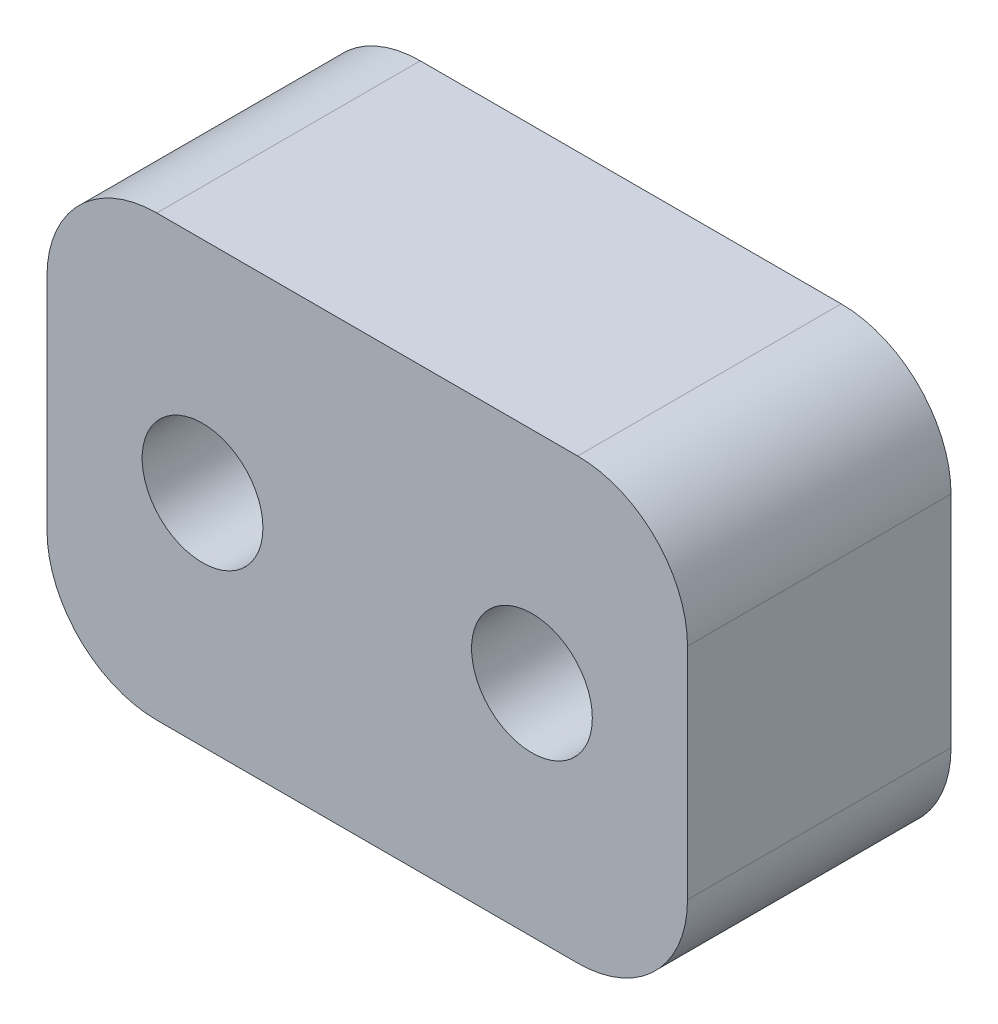
SolidWorks part; units mm, degrees
ref_plane "Front Plane" through (0, 0, 0) normal (0, 0, 1) x (1, 0, 0)
ref_plane "Top Plane" through (0, 0, 0) normal (0, 1, 0) x (1, 0, 0)
ref_plane "Right Plane" through (0, 0, 0) normal (1, 0, 0) x (0, 0, -1)
sketch "Sketch1" plane through (0, 0, 0) normal (0, 0, 1) x (1, 0, 0)
  line L1 (-8.75, 6) -> (8.75, 6)
  line L2 (-8.75, 6) -> (-8.75, -6)
  line L3 (-8.75, -6) -> (8.75, -6)
  line L4 (8.75, 6) -> (8.75, -6)
  line L5 (-8.75, 6) -> (8.75, -6) construction
  line L6 (-8.75, -6) -> (8.75, 6) construction
  point P4 (0, 0)
  dimension "D1" = 17.5
  dimension "D2" = 12
extrude "Boss-Extrude1" add sketch "Sketch1" along normal blind 7.2
fillet "Fillet1" radius 3 4 edges at (8.75, 6, 3.6) (8.75, -6, 3.6) (-8.75, -6, 3.6) (-8.75, 6, 3.6)
sketch "Sketch2" plane through (0, 0, 7.2) normal (0, 0, 1) x (1, 0, 0)
  line L0 (-4.5, 0) -> (4.5, 0) construction
  circle A0 centre (-4.5, 0) radius 1.65
  circle A1 centre (4.5, 0) radius 1.65
  point P4 (0, 0)
  dimension "D2" = 3.3
  dimension "D1" = 9
extrude "Cut-Extrude1" cut sketch "Sketch2" against normal through all
